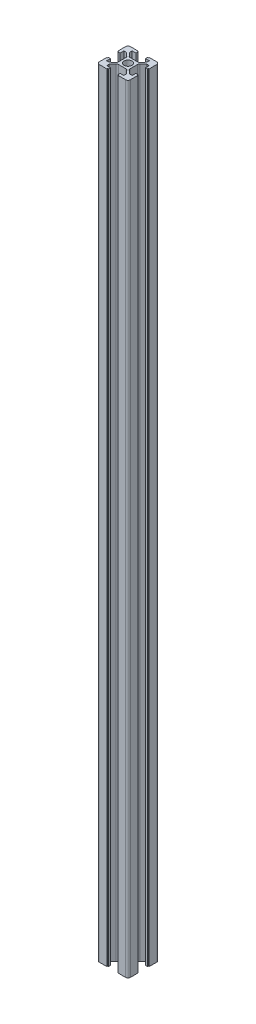
SolidWorks part; units mm, degrees
ref_plane "Front Plane" through (0, 0, 0) normal (0, 0, 1) x (1, 0, 0)
ref_plane "Top Plane" through (0, 0, 0) normal (0, 1, 0) x (1, 0, 0)
ref_plane "Right Plane" through (0, 0, 0) normal (1, 0, 0) x (0, 0, -1)
sketch "Sketch1" plane through (0, 0, 0) normal (0, 1, 0) x (1, 0, 0)
  line L0 (10, 0) -> (3.8, 0) construction
  line L1 (-8.5, -10) -> (8.5, -10)
  line L2 (-10, -8.5) -> (-10, 8.5)
  line L3 (-8.5, 10) -> (8.5, 10)
  line L4 (10, -8.5) -> (10, -3.6)
  line L5 (-10, -10) -> (10, 10) construction
  line L6 (-10, 10) -> (10, -10) construction
  line L7 (3.8, -2.4101) -> (3.8, 2.4101)
  line L8 (9.5, -3.1) -> (9.5, 3.1)
  line L9 (9.5, 3.1) -> (8.2, 3.1)
  line L10 (9.5, 3.1) -> (9.5, 3.6)
  line L11 (9.5, -3.1) -> (9.5, -3.6)
  line L12 (9.5, -3.6) -> (10, -3.6)
  line L13 (9.5, 3.6) -> (10, 3.6)
  line L14 (10, 3.6) -> (10, 8.5)
  line L15 (9.5, -3.1) -> (8.2, -3.1)
  line L16 (8.2, -3.1) -> (3.8, -3.1) construction
  line L17 (8.2, 3.1) -> (3.8, 3.1) construction
  line L18 (8.2, 3.1) -> (8.2, 5.5)
  line L19 (8.2, -3.1) -> (8.2, -5.5)
  line L20 (8.2, -5.5) -> (6.6, -5.5)
  line L21 (8.2, 5.5) -> (6.6, 5.5)
  line L22 (6.6, 5.5) -> (4.3238, 3.549)
  line L23 (6.6, -5.5) -> (4.3238, -3.549)
  line L24 (-5.5, -6.6) -> (-3.549, -4.3238)
  line L25 (-5.5, -8.2) -> (-5.5, -6.6)
  line L26 (-3.1, -8.2) -> (-5.5, -8.2)
  line L27 (-2.4101, -3.8) -> (2.4101, -3.8)
  line L28 (5.5, -6.6) -> (3.549, -4.3238)
  line L29 (5.5, -8.2) -> (5.5, -6.6)
  line L30 (3.1, -8.2) -> (5.5, -8.2)
  line L31 (3.1, -9.5) -> (3.1, -8.2)
  line L32 (3.1, -9.5) -> (3.6, -9.5)
  line L33 (3.6, -9.5) -> (3.6, -10)
  line L34 (-3.6, -9.5) -> (-3.6, -10)
  line L35 (-3.1, -9.5) -> (-3.6, -9.5)
  line L36 (-3.1, -9.5) -> (-3.1, -8.2)
  line L37 (-6.6, 5.5) -> (-4.3238, 3.549)
  line L38 (-8.2, 5.5) -> (-6.6, 5.5)
  line L39 (-8.2, 3.1) -> (-8.2, 5.5)
  line L40 (-3.8, 2.4101) -> (-3.8, -2.4101)
  line L41 (-6.6, -5.5) -> (-4.3238, -3.549)
  line L42 (-8.2, -5.5) -> (-6.6, -5.5)
  line L43 (-8.2, -3.1) -> (-8.2, -5.5)
  line L44 (-9.5, -3.1) -> (-8.2, -3.1)
  line L45 (-9.5, -3.1) -> (-9.5, -3.6)
  line L46 (-9.5, -3.6) -> (-10, -3.6)
  line L47 (-9.5, 3.6) -> (-10, 3.6)
  line L48 (-9.5, 3.1) -> (-9.5, 3.6)
  line L49 (-9.5, 3.1) -> (-8.2, 3.1)
  line L50 (5.5, 6.6) -> (3.549, 4.3238)
  line L51 (5.5, 8.2) -> (5.5, 6.6)
  line L52 (3.1, 8.2) -> (5.5, 8.2)
  line L53 (2.4101, 3.8) -> (-2.4101, 3.8)
  line L54 (-5.5, 6.6) -> (-3.549, 4.3238)
  line L55 (-5.5, 8.2) -> (-5.5, 6.6)
  line L56 (-3.1, 8.2) -> (-5.5, 8.2)
  line L57 (-3.1, 9.5) -> (-3.1, 8.2)
  line L58 (-3.1, 9.5) -> (-3.6, 9.5)
  line L59 (-3.6, 9.5) -> (-3.6, 10)
  line L60 (3.6, 9.5) -> (3.6, 10)
  line L61 (3.1, 9.5) -> (3.6, 9.5)
  line L62 (3.1, 9.5) -> (3.1, 8.2)
  circle A0 centre (0, 0) radius 2.5
  arc A1 (8.5, 10) -> (10, 8.5) centre (8.5, 8.5) cw
  arc A2 (8.5, -10) -> (10, -8.5) centre (8.5, -8.5) ccw
  arc A3 (-8.5, -10) -> (-10, -8.5) centre (-8.5, -8.5) cw
  arc A4 (-10, 8.5) -> (-8.5, 10) centre (-8.5, 8.5) cw
  arc A5 (3.8, -2.4101) -> (4.3238, -3.549) centre (5.3, -2.4101) ccw
  arc A6 (4.3238, 3.549) -> (3.8, 2.4101) centre (5.3, 2.4101) ccw
  arc A7 (-2.4101, -3.8) -> (-3.549, -4.3238) centre (-2.4101, -5.3) ccw
  arc A8 (3.549, -4.3238) -> (2.4101, -3.8) centre (2.4101, -5.3) ccw
  arc A9 (-3.8, 2.4101) -> (-4.3238, 3.549) centre (-5.3, 2.4101) ccw
  arc A10 (-4.3238, -3.549) -> (-3.8, -2.4101) centre (-5.3, -2.4101) ccw
  arc A11 (2.4101, 3.8) -> (3.549, 4.3238) centre (2.4101, 5.3) ccw
  arc A12 (-3.549, 4.3238) -> (-2.4101, 3.8) centre (-2.4101, 5.3) ccw
  point P0 (0, 0)
  point P25 (3.8, 0)
  point P28 (8.5, 0)
  dimension "D3" = 5
  dimension "D4" = 1.5
  dimension "D5" = 1.5
  dimension "D1" = 20
  dimension "D2" = 20
  dimension "D6" = 6.2
  dimension "D7" = 6.2
  dimension "D8" = 0.5
  dimension "D9" = 1.3
  dimension "D10" = 4
extrude "Boss-Extrude1" add sketch "Sketch1" along normal blind 500 contours A12 L54 L55 L56 L57 L58 L59 L3 A4 L2 L47 L48 L49 L39 L38 L37 A9 L40 A10 L41 L42 L43 L44 L45 L46 A3 L1 L34 L35 L36 L26 L25 L24 A7 L27 A8 L28 L29 L30 L31 L32 L33 A2 L4 L12 L11 L15 L19 L20
sketch "Sketch2" plane through (0, 0, 3.8) normal (0, 0, 1) x (1, 0, 0)
  line L0 (0, 500) -> (0, 0) construction
  line L1 (-2.4101, 500) -> (2.4101, 500) construction
  circle A0 centre (0, 450) radius 3
  circle A1 centre (0, 370) radius 3
  circle A2 centre (0, 290) radius 3
  circle A3 centre (0, 210) radius 3
  circle A4 centre (0, 130) radius 3
  circle A5 centre (0, 50) radius 3
  point P7 (27.0253, 465.2814)
  point P18 (0, 0)
  point P19 (0, 0)
  point P20 (0, 0)
  point P21 (0, 0)
  point P22 (0, 0)
  point P23 (0, 0)
  point P24 (0, 0)
  dimension "D1" = 50
  dimension "D2" = 80
  dimension "D3" = 80
  dimension "D4" = 80
  dimension "D5" = 80
  dimension "D6" = 80
extrude "Cut-Extrude1" cut sketch "Sketch2" against normal blind 10
